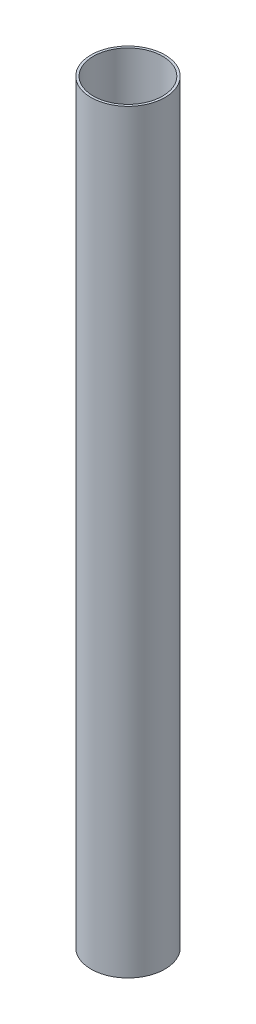
SolidWorks part; units mm, degrees
material "Phenolic Fiber Filled"
ref_plane "Front Plane" through (0, 0, 0) normal (0, 0, 1) x (1, 0, 0)
ref_plane "Top Plane" through (0, 0, 0) normal (0, 1, 0) x (1, 0, 0)
ref_plane "Right Plane" through (0, 0, 0) normal (1, 0, 0) x (0, 0, -1)
sketch "Sketch1" plane through (0, 0, 0) normal (0, 1, 0) x (1, 0, 0)
  circle A0 centre (0, 0) radius 45.847
  circle A1 centre (0, 0) radius 42.926
  dimension "D1" = 91.694
  dimension "D2" = 2.921
extrude "Extrude1" add sketch "Sketch1" along normal blind 936.625
